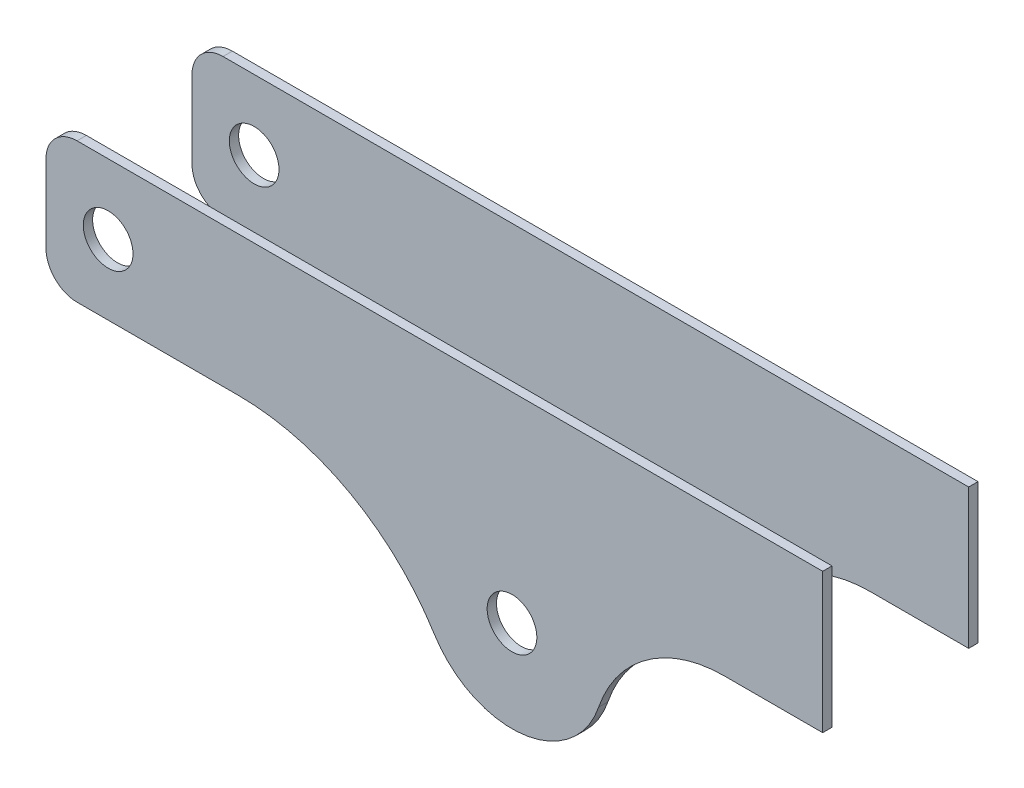
SolidWorks part; units mm, degrees
material "6061-T6 (SS)"
ref_plane "Front Plane" through (0, 0, 0) normal (0, 0, 1) x (1, 0, 0)
ref_plane "Top Plane" through (0, 0, 0) normal (0, 1, 0) x (1, 0, 0)
ref_plane "Right Plane" through (0, 0, 0) normal (1, 0, 0) x (0, 0, -1)
sketch "Sketch1" plane through (0, 0, 0) normal (0, 0, 1) x (1, 0, 0)
  line L0 (0, -10) -> (0, -35)
  line L1 (10, -45) -> (61.8323, -45)
  line L7 (218.3081, -45) -> (250, -45)
  line L8 (250, -45) -> (250, 0)
  line L9 (250, 0) -> (10, 0)
  arc A0 (61.8323, -45) -> (125.0124, -80.0484) centre (61.8323, -119.4702) cw
  arc A1 (177.8826, -73.9455) -> (218.3081, -45) centre (218.3081, -87.702) cw
  arc A2 (125.0124, -80.0484) -> (177.8826, -73.9455) centre (150, -64.4572) ccw
  arc A3 (0, -35) -> (10, -45) centre (10, -35) ccw
  arc A4 (0, -10) -> (10, 0) centre (10, -10) cw
  circle A5 centre (20, -22.5) radius 8
  circle A6 centre (150, -64.4572) radius 8
  point P17 (0, -45)
  point P20 (0, 0)
  dimension "D4" = 10
  dimension "D6" = 16
  dimension "D8" = 16
  dimension "D1" = 150
  dimension "D2" = 100
  dimension "D3" = 45
  dimension "D5" = 45
  dimension "D7" = 20
extrude "Boss-Extrude1" add sketch "Sketch1" along normal blind 3
sketch "Sketch2" plane through (0, 0, 3) normal (0, 0, 1) x (1, 0, 0)
  line L0 (25, 0) -> (250, 0)
  line L1 (25, 0) -> (25, 3)
  line L2 (250, 0) -> (250, 3)
  line L3 (25, 3) -> (250, 3)
  line L4 (250, 0) -> (10, 0) construction
  line L5 (0, -10) -> (0, -35) construction
  line L6 (250, -45) -> (250, 0) construction
  dimension "D1" = 3
  dimension "D2" = 25
  dimension "D3" = 0
extrude "Boss-Extrude2" add sketch "Sketch2" against normal blind 50
sketch "Sketch3" plane through (0, 0, -47) normal (0, 0, -1) x (-1, 0, 0)
  line L6 (-61.8323, -45) -> (-10, -45)
  line L7 (0, -35) -> (0, -10)
  line L8 (-10, 0) -> (-25, 0)
  line L9 (-25, 0) -> (-250, 0)
  line L10 (-250, 0) -> (-250, -45)
  line L11 (-250, -45) -> (-218.3081, -45)
  line L12 (-61.8323, -45) -> (-10, -45)
  line L13 (0, -35) -> (0, -10)
  line L14 (-10, 0) -> (-25, 0)
  line L15 (-25, 0) -> (-250, 0)
  line L16 (-250, 0) -> (-250, -45)
  line L17 (-250, -45) -> (-218.3081, -45)
  circle A0 centre (-20, -22.5) radius 8 construction
  circle A1 centre (-150, -64.4572) radius 8 construction
  circle A2 centre (-20, -22.5) radius 8
  circle A3 centre (-150, -64.4572) radius 8
  arc A5 (-61.8323, -45) -> (-125.0124, -80.0484) centre (-61.8323, -119.4702) ccw
  arc A6 (-10, -45) -> (0, -35) centre (-10, -35) ccw
  arc A7 (0, -10) -> (-10, 0) centre (-10, -10) ccw
  arc A8 (-177.8826, -73.9455) -> (-218.3081, -45) centre (-218.3081, -87.702) ccw
  arc A9 (-177.8826, -73.9455) -> (-125.0124, -80.0484) centre (-150, -64.4572) ccw
  arc A10 (-61.8323, -45) -> (-125.0124, -80.0484) centre (-61.8323, -119.4702) ccw
  arc A11 (-10, -45) -> (0, -35) centre (-10, -35) ccw
  arc A12 (0, -10) -> (-10, 0) centre (-10, -10) ccw
  arc A13 (-177.8826, -73.9455) -> (-218.3081, -45) centre (-218.3081, -87.702) ccw
  arc A14 (-177.8826, -73.9455) -> (-125.0124, -80.0484) centre (-150, -64.4572) ccw
  dimension "D1" = 0
extrude "Boss-Extrude3" add sketch "Sketch3" against normal blind 3
sketch "Sketch4" plane through (0, 3, 0) normal (0, 1, 0) x (1, 0, 0)
  line L0 (25, 47) -> (25, -3) construction
  line L1 (250, 47) -> (25, 47) construction
  line L2 (25, 22) -> (56.3581, 22) construction
  circle A0 centre (130, 34) radius 2
  circle A2 centre (130, 10) radius 2
  circle A3 centre (143, 34) radius 2
  circle A4 centre (143, 10) radius 2
  circle A5 centre (156, 34) radius 2
  circle A6 centre (156, 10) radius 2
  dimension "D1" = 4
  dimension "D2" = 105
  dimension "D3" = 13
extrude "Cut-Extrude1" cut sketch "Sketch4" against normal blind 3
sketch "Sketch5" plane through (0, 3, 0) normal (0, 1, 0) x (1, 0, 0)
  line L0 (25, 47) -> (250, 47)
  line L1 (25, 47) -> (25, -3.3248)
  line L2 (250, 47) -> (250, -3.3248)
  line L3 (25, -3.3248) -> (250, -3.3248)
extrude "Cut-Extrude2" cut sketch "Sketch5" against normal blind 3
